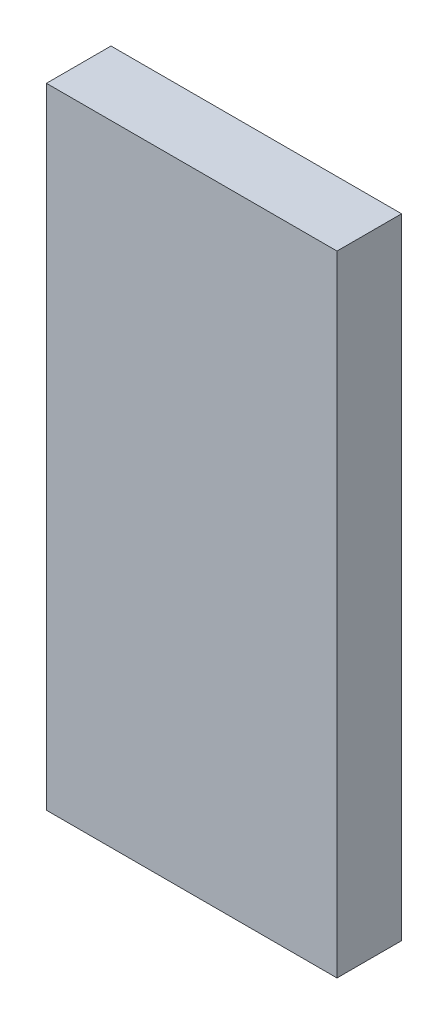
SolidWorks part; units mm, degrees
material "Silicon Rubber"
ref_plane "Front Plane" through (0, 0, 0) normal (0, 0, 1) x (1, 0, 0)
ref_plane "Top Plane" through (0, 0, 0) normal (0, 1, 0) x (1, 0, 0)
ref_plane "Right Plane" through (0, 0, 0) normal (1, 0, 0) x (0, 0, -1)
sketch "Sketch1" plane through (0, 0, 0) normal (0, 0, 1) x (1, 0, 0)
  line L0 (0, 0) -> (0, 39)
  line L1 (0, 39) -> (18, 39)
  line L2 (18, 39) -> (18, 0)
  line L3 (18, 0) -> (0, 0)
  dimension "D1" = 18
  dimension "D2" = 39
extrude "Boss-Extrude1" add sketch "Sketch1" along normal blind 4
